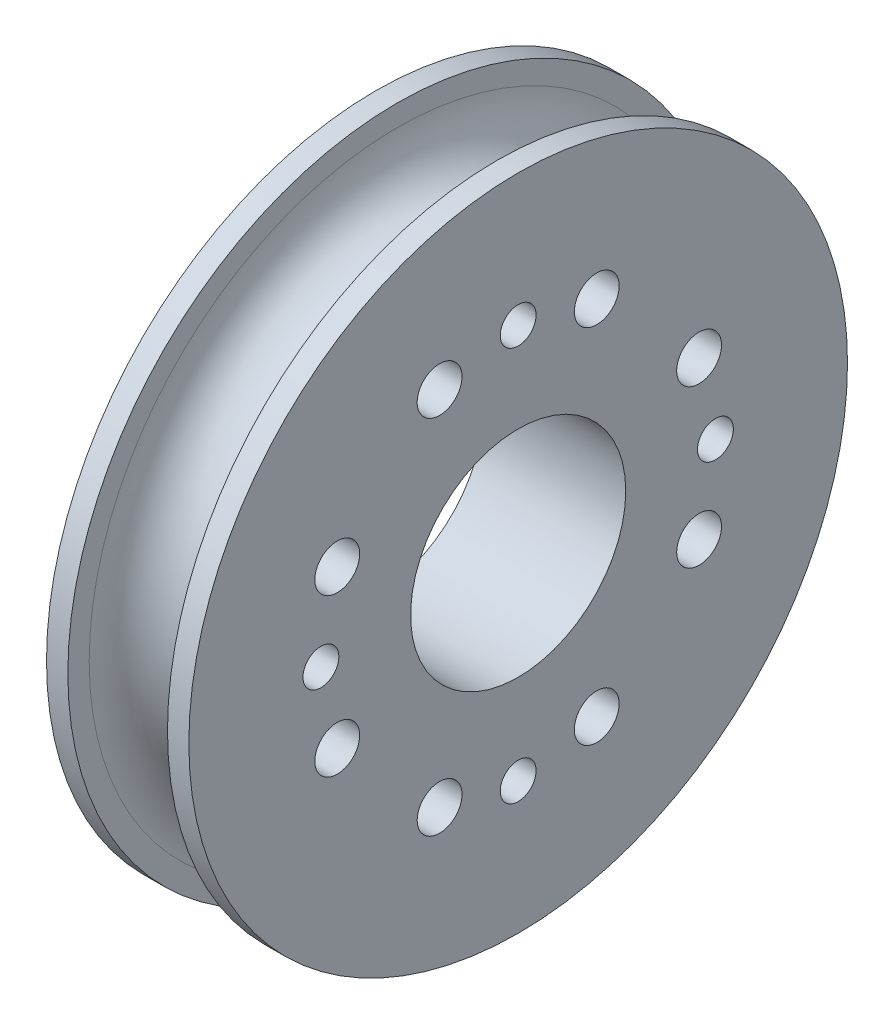
SolidWorks part; units mm, degrees
ref_plane "Front Plane" through (0, 0, 0) normal (0, 0, 1) x (1, 0, 0)
ref_plane "Top Plane" through (0, 0, 0) normal (0, 1, 0) x (1, 0, 0)
ref_plane "Right Plane" through (0, 0, 0) normal (1, 0, 0) x (0, 0, -1)
sketch "Sketch1" plane through (0, 0, 0) normal (0, 0, 1) x (1, 0, 0)
  line L1 (0, 0) -> (7.9375, 0)
  line L2 (0, 0) -> (0, 14)
  line L4 (7.9375, 0) -> (7.9375, 14)
  line L5 (7.9375, 17.175) -> (7.9375, 14)
  line L6 (0, 17.175) -> (0, 14)
  line L9 (1.1906, 17.175) -> (1.1906, 18.3656)
  line L10 (1.1906, 18.3656) -> (0, 18.3656)
  line L11 (0, 17.175) -> (0, 18.3656)
  line L13 (7.9375, 17.175) -> (7.9375, 18.3656)
  line L14 (7.9375, 18.3656) -> (6.7469, 18.3656)
  line L15 (6.7469, 17.175) -> (6.7469, 18.3656)
  arc A0 (1.1906, 17.175) -> (6.7469, 17.175) centre (3.9687, 17.175) ccw
  dimension "D3" = 5.5562
  dimension "D1" = 7.9375
  dimension "D2" = 14
  dimension "D4" = 1.1906
  dimension "D5" = 1.1906
revolve "Revolve1" add sketch "Sketch1" angle 360 about L1
sketch "Sketch3" plane through (7.9375, 0, 0) normal (1, 0, 0) x (0, 0, -1)
  circle A0 centre (0, 0) radius 6
  dimension "D1" = 12
extrude "Extrude1" cut sketch "Sketch3" against normal through all
sketch "Sketch4" plane through (7.9375, 0, 0) normal (1, 0, 0) x (0, 0, -1)
  line L0 (0, -23.8998) -> (0, 29.2964) construction
  line L1 (31.7409, 0) -> (-31.7451, 0) construction
  line L2 (0, 0) -> (18.9307, 32.789) construction
  line L3 (0, 0) -> (-17.3596, 30.0677) construction
  circle A0 centre (0, 11) radius 1
  circle A1 centre (-4.3818, 10.0896) radius 1.25
  circle A2 centre (4.3818, 10.0896) radius 1.25
  circle A3 centre (10.0896, -4.3818) radius 1.25
  circle A4 centre (11, 0) radius 1
  circle A5 centre (10.0896, 4.3818) radius 1.25
  circle A6 centre (-4.3818, -10.0896) radius 1.25
  circle A7 centre (0, -11) radius 1
  circle A8 centre (4.3818, -10.0896) radius 1.25
  circle A9 centre (-10.0896, 4.3818) radius 1.25
  circle A10 centre (-11, 0) radius 1
  circle A11 centre (-10.0896, -4.3818) radius 1.25
  dimension "D1" = 2
  dimension "D5" = 2.5
  dimension "D2" = 11
  dimension "D4" = 30
  dimension "D6" = 11
extrude "Extrude2" cut sketch "Sketch4" against normal through all
